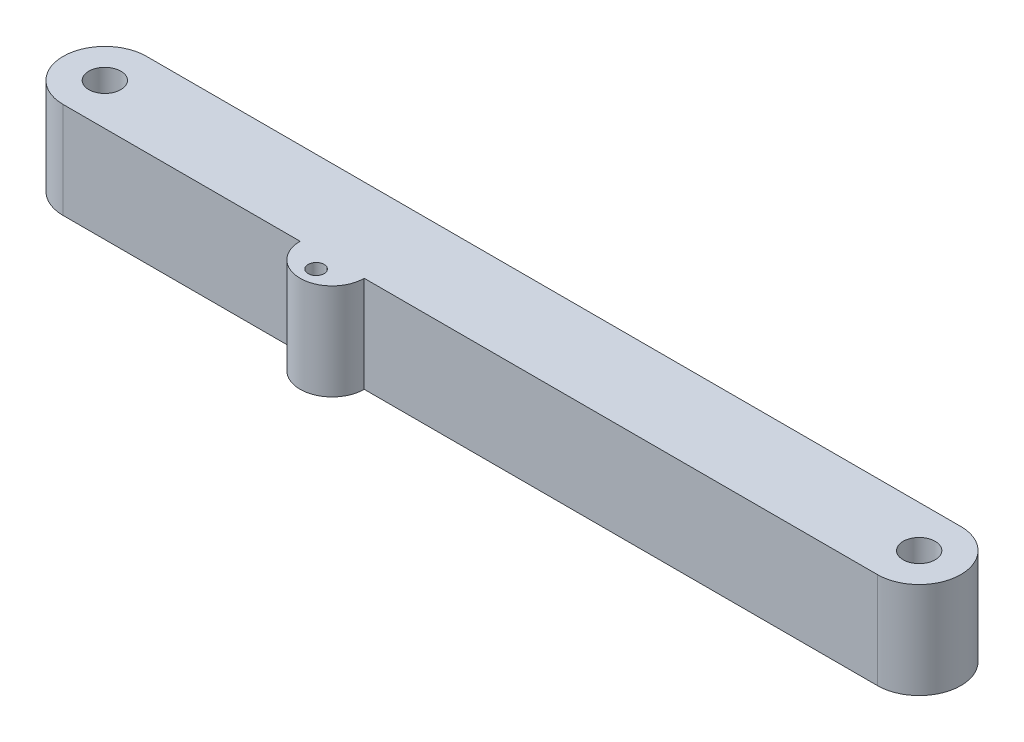
SolidWorks part; units mm, degrees
ref_plane "Front Plane" through (0, 0, 0) normal (0, 0, 1) x (1, 0, 0)
ref_plane "Top Plane" through (0, 0, 0) normal (0, 1, 0) x (1, 0, 0)
ref_plane "Right Plane" through (0, 0, 0) normal (1, 0, 0) x (0, 0, -1)
sketch "Sketch1" plane through (0, 0, 0) normal (0, 1, 0) x (1, 0, 0)
  line L0 (0, 0) -> (34315.2938, 0) construction
  line L1 (0, 0) -> (0, 34315.2938) construction
  line L2 (-80.645, -8.255) -> (80.645, -8.255)
  line L3 (-80.645, 8.255) -> (80.645, 8.255)
  arc A1 (-80.645, 8.255) -> (-80.645, -8.255) centre (-80.645, 0) ccw
  arc A2 (80.645, 8.255) -> (80.645, -8.255) centre (80.645, 0) cw
  circle A3 centre (-80.645, 0) radius 3.175
  circle A4 centre (80.645, 0) radius 3.175
  point P2 (-88.9, 0)
  point P7 (88.9, 0)
  point P13 (0, -8.255)
  point P16 (0, 8.255)
  dimension "D2" = 177.8
  dimension "D3" = 6.35
  dimension "D1" = 16.51
extrude "Boss-Extrude1" add sketch "Sketch1" along normal blind 19.05
sketch "Sketch2" plane through (0, 19.05, 0) normal (0, 1, 0) x (1, 0, 0)
  line L0 (0, 0) -> (50000, 0) construction
  line L1 (-27.3639, 0) -> (-27.3639, -8.255)
  line L2 (-80.645, -8.255) -> (80.645, -8.255)
  line L3 (80.645, 8.255) -> (-80.645, 8.255)
  line L4 (-80.645, -8.255) -> (80.645, -8.255)
  line L5 (80.645, 8.255) -> (-80.645, 8.255)
  line L6 (-27.3639, -14.605) -> (49972.6361, -14.605) construction
  circle A0 centre (-27.3639, -8.255) radius 6.35
  circle A1 centre (-27.3639, -11.43) radius 1.5875
  arc A2 (-80.645, 8.255) -> (-80.645, -8.255) centre (-80.645, 0) ccw
  arc A3 (80.645, -8.255) -> (80.645, 8.255) centre (80.645, 0) ccw
  arc A4 (-80.645, 8.255) -> (-80.645, -8.255) centre (-80.645, 0) ccw
  arc A5 (80.645, -8.255) -> (80.645, 8.255) centre (80.645, 0) ccw
  point P16 (-27.3639, -14.605)
  line M8 (-80.645, -8.255) -> (80.645, -8.255)
  dimension "D3" = 12.7
  dimension "D4" = 3.175
  dimension "D5" = 3.175
  dimension "D2" = 53.2811
  dimension "D1" = 0
extrude "Boss-Extrude2" add sketch "Sketch2" along direction (0, 1, 0) on the side against the normal up to surface (19.05 mm away) contours L4 A0 L1 | L1 A0 M8
